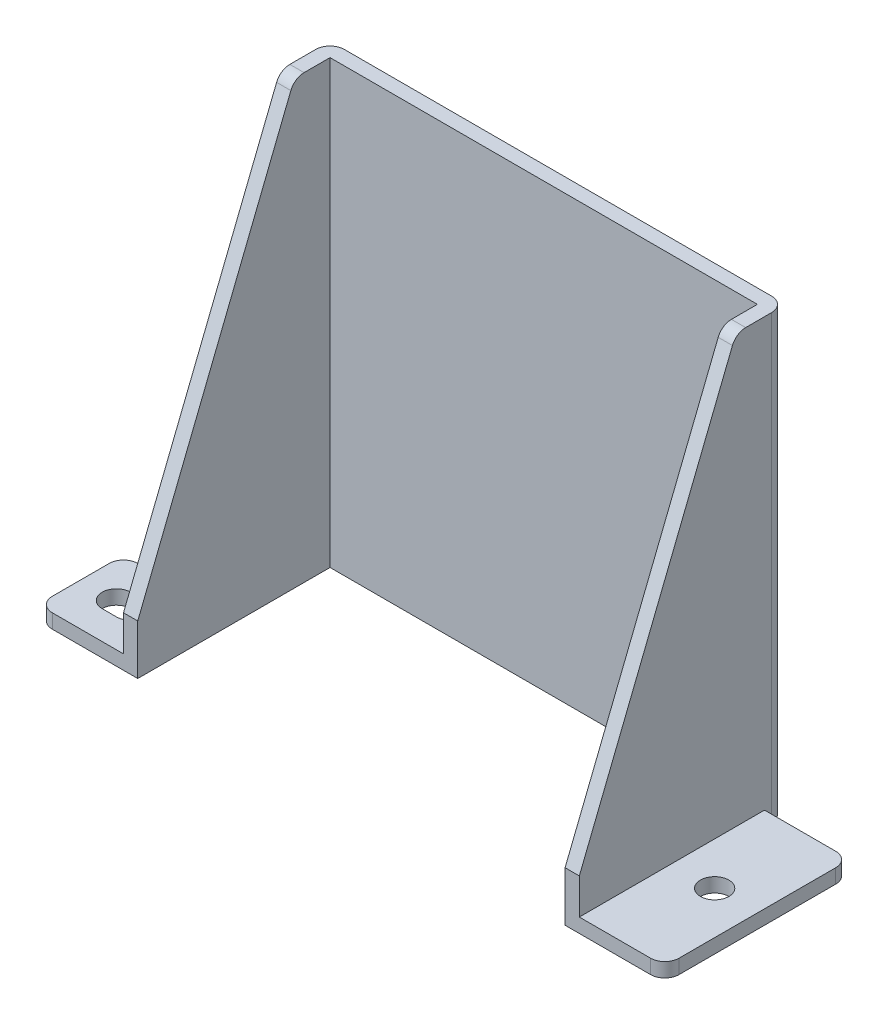
SolidWorks part; units mm, degrees
ref_plane "Alzado" through (0, 0, 0) normal (0, 0, 1) x (1, 0, 0)
ref_plane "Planta" through (0, 0, 0) normal (0, 1, 0) x (1, 0, 0)
ref_plane "Vista lateral" through (0, 0, 0) normal (1, 0, 0) x (0, 0, -1)
sketch "Croquis1" plane through (0, 0, 0) normal (0, 1, 0) x (1, 0, 0)
  line L0 (-32, -2.5) -> (-32, 14.5)
  line L1 (-44, -14.5) -> (-30, -14.5)
  line L2 (-44, -14.5) -> (-44, -2.5)
  line L3 (-32, 14.5) -> (32, 14.5)
  line L4 (44, -14.5) -> (44, 14.5) construction
  line L5 (-44, -14.5) -> (44, 14.5) construction
  line L6 (-44, 14.5) -> (44, -14.5) construction
  line L7 (-44, -14.5) -> (-32, -14.5)
  line L8 (-44, -14.5) -> (-44, -2.5)
  line L9 (-44, -2.5) -> (-32, -2.5)
  line L10 (-32, -14.5) -> (-32, -2.5) construction
  line L12 (44, 14.5) -> (44, -14.5) construction
  line L13 (44, -14.5) -> (32, -14.5)
  line L14 (32, 14.5) -> (32, -14.5) construction
  line L15 (-30, -14.5) -> (-30, 12.5)
  line L16 (-30, 12.5) -> (30, 12.5)
  line L17 (30, 12.5) -> (30, -14.5)
  line L18 (30, -14.5) -> (44, -14.5)
  line L19 (-44, 14.5) -> (-44, -14.5) construction
  line L20 (44, -14.5) -> (44, 11.5)
  line L21 (44, 11.5) -> (32, 11.5)
  line L22 (32, 11.5) -> (32, 14.5)
  line L23 (0, 0) -> (0, -14.5) construction
  point P0 (0, 0)
  point P15 (0, 12.5)
  point P21 (0, 0)
  dimension "D1" = 60
  dimension "D2" = 12
  dimension "D3" = 12
  dimension "D4" = 29
  dimension "D5" = 12
  dimension "D6" = 14
  dimension "D7" = 2
  dimension "D9" = 26
extrude "Saliente-Extruir1" add sketch "Croquis1" along normal blind 2 contours L17 L18 L13 L4 L3 L0 L9 L2 L1 L15 L16
sketch "Croquis2" plane through (0, 2, 0) normal (0, 1, 0) x (1, 0, 0)
  line L0 (-32, -2.5) -> (-32, 14.5) construction
  line L1 (-32, -2.5) -> (-32, 14.5)
  line L2 (-32, 14.5) -> (32, 14.5) construction
  line L3 (-32, 14.5) -> (32, 14.5)
  line L4 (32, 14.5) -> (32, -14.5) construction
  line L5 (32, 14.5) -> (32, -14.5)
  line L6 (30, -14.5) -> (44, -14.5) construction
  line L7 (30, -14.5) -> (32, -14.5)
  line L8 (-44, -14.5) -> (-30, -14.5) construction
  line L9 (-32, -14.5) -> (-32, -2.5) construction
  line L10 (-30, -14.5) -> (-30, 12.5) construction
  line L11 (-30, 12.5) -> (30, 12.5) construction
  line L12 (30, 12.5) -> (30, -14.5) construction
  line L13 (-32, -14.5) -> (-30, -14.5)
  line L14 (-32, -14.5) -> (-32, -2.5)
  line L15 (-30, -14.5) -> (-30, 12.5)
  line L16 (-30, 12.5) -> (30, 12.5)
  line L17 (30, 12.5) -> (30, -14.5)
  line M1 (30, 12.5) -> (30, -14.5)
  line M2 (30, -14.5) -> (44, -14.5)
  line M5 (-32, 14.5) -> (-32, -2.5)
  line M8 (-44, -14.5) -> (-30, -14.5)
  line M9 (-30, -14.5) -> (-30, 12.5)
  line M10 (-30, 12.5) -> (30, 12.5)
extrude "Saliente-Extruir2" add sketch "Croquis2" along normal blind 60 contours L14 L5 L3 M8 M9 M10 M1 M2 M5
sketch "Croquis3" plane through (0, 0, 0) normal (1, 0, 0) x (0, 0, -1)
  line L0 (-14.5, 2) -> (-14.5, 7) construction
  line L1 (-14.5, 62) -> (-14.5, 2) construction
  line L2 (-14.5, 7) -> (7.5, 62)
  line L3 (14.5, 62) -> (7.5, 62) construction
  line L4 (14.5, 62) -> (-14.5, 62) construction
  line L5 (7.5, 62) -> (-14.5, 62)
  line L6 (-14.5, 62) -> (-14.5, 7)
  line L7 (-14.5, 0) -> (-2.5, 0) construction
  dimension "D1" = 7
  dimension "D2" = 5
  dimension "D3" = 2
extrude "Cortar-Extruir1" cut sketch "Croquis3" against normal through all both and the other way through all
sketch "Croquis4" plane through (0, 2, 0) normal (0, 1, 0) x (1, 0, 0)
  line L0 (38, -14.5) -> (38, 11.5) construction
  line L1 (-44, -2.5) -> (-32, -14.5) construction
  line L2 (-39, -8.5) -> (-37, -8.5) construction
  line L3 (-39, -6.5) -> (-37, -6.5)
  line L4 (-39, -10.5) -> (-37, -10.5)
  line L9 (44, -14.5) -> (44, 14.5) construction
  line L10 (32, -14.5) -> (44, -14.5) construction
  line L11 (32, -14.5) -> (32, 11.5) construction
  line L12 (32, 11.5) -> (44, 11.5) construction
  line L13 (44, -14.5) -> (44, 11.5) construction
  arc A1 (-39, -6.5) -> (-39, -10.5) centre (-39, -8.5) ccw
  arc A2 (-37, -10.5) -> (-37, -6.5) centre (-37, -8.5) ccw
  circle A3 centre (38, -1.5) radius 2
  point P12 (-38, -8.5)
  point P18 (0, 0)
  point P20 (0, 0)
  point P21 (0, 0)
  dimension "D1" = 4
  dimension "D3" = 2
  dimension "D2" = 2
  dimension "D8" = 26
extrude "Cortar-Extruir2" cut sketch "Croquis4" against normal through all
fillet "Redondeo1" radius 2 8 edges at (-32, 31, -14.5) (32, 31, -14.5) (-44, 1, 2.5) (-44, 1, 14.5) (31, 62, -7.5) (-31, 62, -7.5) (44, 1, -11.5) (44, 1, 14.5)
fillet "Redondeo2" [suppressed] radius 1
sketch "Croquis6" plane through (0, 2, 0) normal (0, 1, 0) x (1, 0, 0)
  line L0 (-44, -14.5) -> (-32, -14.5) construction
  line L1 (-32, -14.5) -> (-38, -14.5) construction
  line L2 (-38, -6.5) -> (-38, -10.5) construction
  line L3 (-37, -6.5) -> (-39, -6.5) construction
  line L4 (-39, -10.5) -> (-37, -10.5) construction
  line L5 (-38, -8.5) -> (-38, -14.5) construction
  line L6 (38, -1.5) -> (44, -1.5) construction
  line L7 (44, -14.5) -> (44, 11.5) construction
  line L8 (38, -1.5) -> (38, -14.5) construction
  line L10 (44, -14.5) -> (32, -14.5) construction
